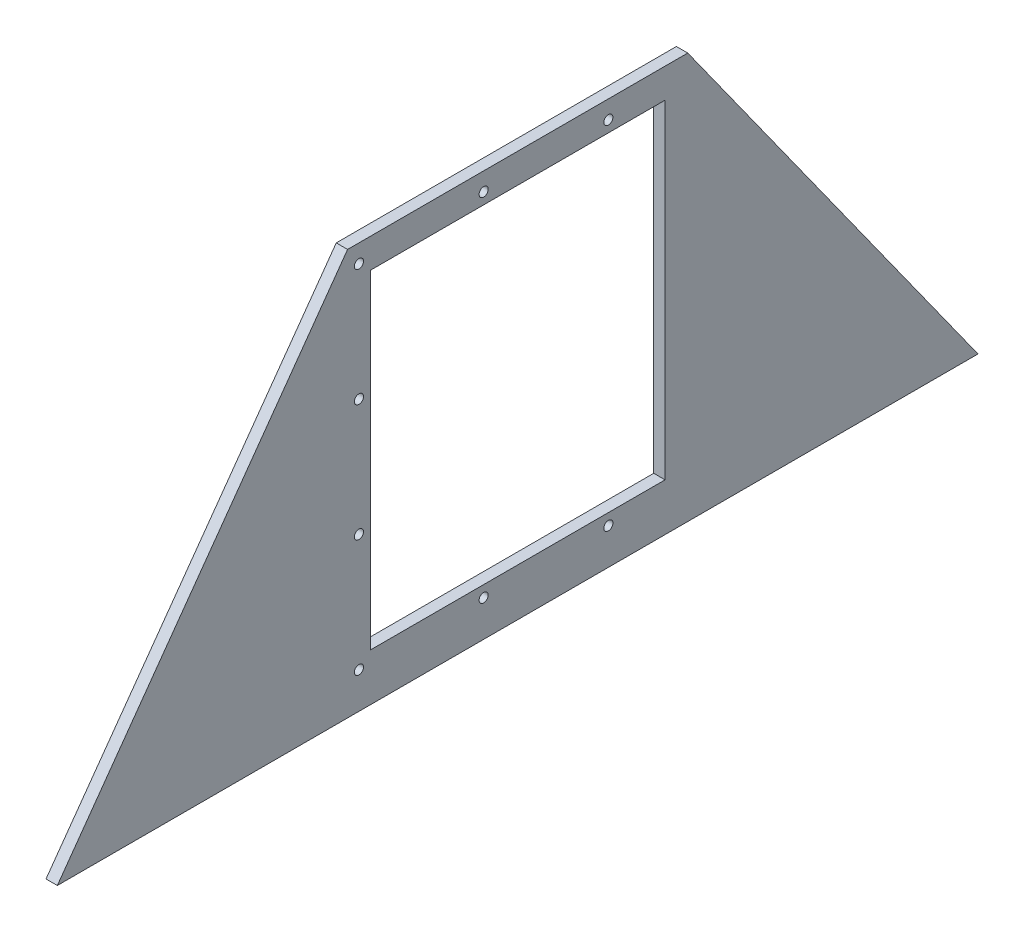
SolidWorks part; units mm, degrees
ref_plane "Front Plane" through (0, 0, 0) normal (0, 0, 1) x (1, 0, 0)
ref_plane "Top Plane" through (0, 0, 0) normal (0, 1, 0) x (1, 0, 0)
ref_plane "Right Plane" through (0, 0, 0) normal (1, 0, 0) x (0, 0, -1)
sketch "Sketch1" plane through (0, 0, 0) normal (1, 0, 0) x (0, 0, -1)
  line L0 (257.81, 0) -> (-257.81, 0)
  line L2 (-257.81, 0) -> (-95.25, 227.2413)
  line L3 (-95.25, 227.2413) -> (95.25, 227.2413)
  line L4 (257.81, 0) -> (95.25, 227.2413)
  point P4 (0, 227.2413)
  point P5 (0, 0)
  dimension "D1" = 279.4
  dimension "D2" = 515.62
  dimension "D3" = 190.5
extrude "Boss-Extrude1" add sketch "Sketch1" along normal blind 6.35
sketch "Sketch2" plane through (6.35, 0, 0) normal (1, 0, 0) x (0, 0, -1)
  line L0 (95.25, 227.2413) -> (-95.25, 227.2413) construction
  circle A0 centre (277.9565, 163.7413) radius 6.35
  dimension "D1" = 12.7
  dimension "D2" = 63.5
sketch "Sketch3" plane through (6.35, 0, 0) normal (1, 0, 0) x (0, 0, -1)
  line L0 (95.25, 227.2413) -> (-95.25, 227.2413) construction
  line L1 (-82.55, 210.7313) -> (82.55, 210.7313)
  line L2 (-82.55, 210.7313) -> (-82.55, 26.5813)
  line L3 (-82.55, 26.5813) -> (82.55, 26.5813)
  line L4 (82.55, 210.7313) -> (82.55, 26.5813)
  point P4 (0, 210.7313)
  point P7 (0, 227.2413)
  dimension "D1" = 165.1
  dimension "D2" = 16.51
  dimension "D3" = 184.15
extrude "Cut-Extrude1" cut sketch "Sketch3" against normal through all
hole_wizard "1/4 Clearance Hole1" positions "Sketch5" profile "Sketch6" hole size "#10" standard "ANSI Inch"
sketch "Sketch5" plane through (0, 0, 0) normal (-1, 0, 0) x (0, 0, 1)
  circle A0 centre (19.05, 217.0813) radius 2.5527 construction
  circle A1 centre (-50.8, 217.0813) radius 2.5527 construction
  circle A2 centre (-50.8, 151.4646) radius 2.5527 construction
  circle A3 centre (-50.8, 85.848) radius 2.5527 construction
  circle A4 centre (-50.8, 20.2313) radius 2.5527 construction
  circle A5 centre (19.05, 20.2313) radius 2.5527 construction
  circle A7 centre (88.9, 20.2313) radius 2.5527 construction
  circle A8 centre (88.9, 85.848) radius 2.5527 construction
  circle A9 centre (88.9, 151.4646) radius 2.5527 construction
  circle A10 centre (88.9, 217.0813) radius 2.5527 construction
  circle A11 centre (19.05, 217.0813) radius 2.5527
  circle A12 centre (-50.8, 217.0813) radius 2.5527
  circle A13 centre (-50.8, 151.4646) radius 2.5527
  circle A14 centre (-50.8, 85.848) radius 2.5527
  circle A15 centre (-50.8, 20.2313) radius 2.5527
  circle A16 centre (19.05, 20.2313) radius 2.5527
  circle A18 centre (88.9, 20.2313) radius 2.5527
  circle A19 centre (88.9, 85.848) radius 2.5527
  circle A20 centre (88.9, 151.4646) radius 2.5527
  circle A21 centre (88.9, 217.0813) radius 2.5527
  point P1 (19.05, 217.0813)
  point P3 (-50.8, 217.0813)
  point P5 (-50.8, 151.4646)
  point P7 (-50.8, 85.848)
  point P9 (-50.8, 20.2313)
  point P11 (19.05, 20.2313)
  point P15 (88.9, 20.2313)
  point P17 (88.9, 85.848)
  point P19 (88.9, 151.4646)
  point P21 (88.9, 217.0813)
sketch "Sketch6" plane through (0, 217.0813, 19.05) normal (0, 1, 0) x (0, 0, 1)
  line L0 (0, 0) -> (0, 26.9338)
  line L1 (0, 26.9338) -> (2.5527, 25.4)
  line L2 (2.5527, 25.4) -> (2.5527, 0)
  line L5 (2.5527, 0) -> (0, 0)
  line L10 (0, 26.9338) -> (-2.5527, 25.4) construction
  line L11 (0, -6.35) -> (0, 107.95) construction
  dimension "Hole Dia." = 5.1054
  dimension "Hole Depth" = 25.4
  dimension "Drill Angle" = 118
